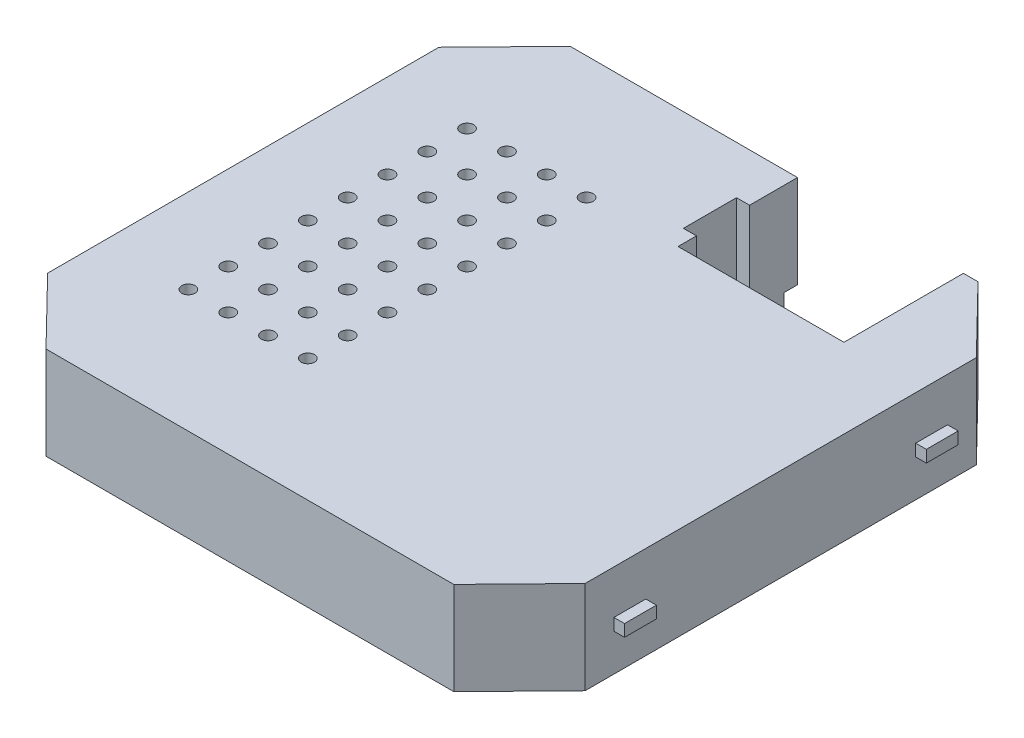
SolidWorks part; units mm, degrees
ref_plane "Front Plane" through (0, 0, 0) normal (0, 0, 1) x (1, 0, 0)
ref_plane "Top Plane" through (0, 0, 0) normal (0, 1, 0) x (1, 0, 0)
ref_plane "Right Plane" through (0, 0, 0) normal (1, 0, 0) x (0, 0, -1)
sketch "Sketch1" plane through (0, 0, 0) normal (0, 1, 0) x (1, 0, 0)
  line L0 (-20.25, 19.75) -> (20.25, 19.75) construction
  line L1 (-20.25, -19.75) -> (20.25, -19.75) construction
  line L2 (20.25, 19.75) -> (20.25, -19.75) construction
  line L3 (20.25, -19.75) -> (-20.25, 19.75) construction
  line L4 (20.25, 19.75) -> (-20.25, -19.75) construction
  line L5 (-20.25, 19.75) -> (-20.25, -19.75) construction
  line L6 (-20.25, 14.7388) -> (-15.3625, 19.75)
  line L7 (-20.25, -14.7388) -> (-15.3625, -19.75)
  line L8 (20.25, -14.7388) -> (15.3625, -19.75)
  line L9 (20.25, 14.7388) -> (15.3625, 19.75)
  line L10 (20.25, -14.7388) -> (20.25, 14.7388)
  line L11 (15.3625, -19.75) -> (-15.3625, -19.75)
  line L12 (-15.3625, 19.75) -> (15.3625, 19.75)
  line L13 (-20.25, 14.7388) -> (-20.25, -14.7388)
  point P5 (0, 0)
  point P13 (0, 0)
  point P14 (0, 0)
  dimension "D1" = 39.5
  dimension "D2" = 40.5
  dimension "D3" = 7
  dimension "D4" = 7
  dimension "D5" = 7
  dimension "D6" = 7
extrude "Boss-Extrude1" add sketch "Sketch1" along normal blind 7
sketch "Sketch2" plane through (0, 0, 0) normal (0, -1, 0) x (1, 0, 0)
  line L44 (14.941, 18.75) -> (-14.941, 18.75)
  line L45 (19.25, 14.3319) -> (14.941, 18.75)
  line L46 (19.25, -14.3319) -> (19.25, 14.3319)
  line L47 (14.941, -18.75) -> (19.25, -14.3319)
  line L48 (-14.941, -18.75) -> (14.941, -18.75)
  line L49 (-19.25, -14.3319) -> (-14.941, -18.75)
  line L50 (-19.25, 14.3319) -> (-19.25, -14.3319)
  line L51 (-14.941, 18.75) -> (-19.25, 14.3319)
  line L52 (14.941, 18.75) -> (-14.941, 18.75)
  line L53 (19.25, 14.3319) -> (14.941, 18.75)
  line L54 (19.25, -14.3319) -> (19.25, 14.3319)
  line L55 (14.941, -18.75) -> (19.25, -14.3319)
  line L56 (-14.941, -18.75) -> (14.941, -18.75)
  line L57 (-19.25, -14.3319) -> (-14.941, -18.75)
  line L58 (-19.25, 14.3319) -> (-19.25, -14.3319)
  line L59 (-14.941, 18.75) -> (-19.25, 14.3319)
  dimension "D1" = 1
extrude "Cut-Extrude1" cut sketch "Sketch2" against normal blind 6
sketch "Sketch3" plane through (0, 7, 0) normal (0, 1, 0) x (1, 0, 0)
  line L0 (15.3625, 19.75) -> (-15.3625, 19.75) construction
  line L1 (14.2625, 19.75) -> (1.7625, 19.75)
  line L2 (14.2625, 19.75) -> (14.2625, 10.75)
  line L3 (14.2625, 10.75) -> (1.7625, 10.75)
  line L5 (1.7625, 19.75) -> (1.7625, 16.137)
  line L6 (1.7625, 16.137) -> (0.7776, 16.137)
  line L7 (0.7776, 16.137) -> (0.7776, 12.137)
  line L8 (0.7776, 12.137) -> (1.7625, 12.137)
  line L9 (1.7625, 12.137) -> (1.7625, 10.75)
  dimension "D1" = 1.1
  dimension "D2" = 9
  dimension "D3" = 12.5
  dimension "D4" = 4
extrude "Cut-Extrude2" cut sketch "Sketch3" against normal through all
sketch "Sketch4" plane through (0, 6, 0) normal (0, -1, 0) x (1, 0, 0)
  line L34 (0.7625, -18.75) -> (1.7625, -18.75)
  line L35 (1.7625, -18.75) -> (1.7625, -16.137)
  line L36 (1.7625, -16.137) -> (0.7776, -16.137)
  line L37 (0.7776, -16.137) -> (0.7776, -12.137)
  line L38 (0.7776, -12.137) -> (1.7625, -12.137)
  line L39 (1.7625, -12.137) -> (1.7625, -10.75)
  line L40 (1.7625, -10.75) -> (14.2625, -10.75)
  line L41 (-0.2224, -17.137) -> (0.7625, -17.137)
  line L42 (-0.2224, -11.137) -> (-0.2224, -17.137)
  line L43 (0.7625, -17.137) -> (0.7625, -18.75)
  line L44 (0.7625, -11.137) -> (-0.2224, -11.137)
  line L45 (0.7625, -9.75) -> (0.7625, -11.137)
  line L46 (15.2625, -18.75) -> (15.2625, -9.75)
  line L47 (15.2625, -9.75) -> (0.7625, -9.75)
  line L48 (-0.2224, -17.137) -> (0.7625, -17.137)
  line L49 (-0.2224, -11.137) -> (-0.2224, -17.137)
  line L50 (0.7625, -17.137) -> (0.7625, -18.75)
  line L51 (0.7625, -11.137) -> (-0.2224, -11.137)
  line L52 (0.7625, -9.75) -> (0.7625, -11.137)
  line L53 (15.2625, -18.75) -> (15.2625, -9.75)
  line L54 (15.2625, -9.75) -> (0.7625, -9.75)
  line L55 (14.2625, -10.75) -> (14.2625, -18.75)
  line L56 (14.2625, -18.75) -> (15.2625, -18.75)
  dimension "D2" = 1
extrude "Boss-Extrude2" add sketch "Sketch4" along normal blind 10
sketch "Sketch5" plane through (-20.25, 0, 0) normal (-1, 0, 0) x (0, 0, 1)
  line L0 (-10.1697, 3.7) -> (-10.1697, 2.8)
  line L1 (-12.8697, 4) -> (-9.8697, 4) construction
  line L2 (-12.8697, 4) -> (-12.8697, 2.5) construction
  line L3 (-12.8697, 2.5) -> (-9.8697, 2.5) construction
  line L4 (-9.8697, 4) -> (-9.8697, 2.5) construction
  line L5 (-12.5697, 2.8) -> (-10.1697, 2.8)
  line L6 (-12.5697, 3.7) -> (-12.5697, 2.8)
  line L7 (-12.5697, 3.7) -> (-10.1697, 3.7)
  line L8 (0, 0) -> (0, 8.3052) construction
  line L11 (12.5697, 3.7) -> (10.1697, 3.7)
  line L12 (12.5697, 3.7) -> (12.5697, 2.8)
  line L13 (12.5697, 2.8) -> (10.1697, 2.8)
  line L14 (10.1697, 3.7) -> (10.1697, 2.8)
  point P18 (0, 0)
  dimension "D1" = 0.3
extrude "Boss-Extrude3" add sketch "Sketch5" along normal blind 0.8
sketch "Sketch6" plane through (20.25, 0, 0) normal (1, 0, 0) x (0, 0, -1)
  line L0 (-12.8697, 4) -> (-12.8697, 2.5) construction
  line L1 (-12.8697, 2.5) -> (-9.8697, 2.5) construction
  line L2 (-9.8697, 2.5) -> (-9.8697, 4) construction
  line L3 (-9.8697, 4) -> (-12.8697, 4) construction
  line L4 (-10.1697, 3.7) -> (-12.5697, 3.7)
  line L5 (-12.5697, 3.7) -> (-12.5697, 2.8)
  line L6 (-12.5697, 2.8) -> (-10.1697, 2.8)
  line L7 (-10.1697, 2.8) -> (-10.1697, 3.7)
  line L8 (0, 0) -> (0, 9.647) construction
  line L9 (10.1697, 2.8) -> (10.1697, 3.7)
  line L10 (12.5697, 2.8) -> (10.1697, 2.8)
  line L11 (12.5697, 3.7) -> (12.5697, 2.8)
  line L12 (10.1697, 3.7) -> (12.5697, 3.7)
  dimension "D1" = 0.3
extrude "Boss-Extrude4" add sketch "Sketch6" along normal blind 0.8
sketch "Sketch7" plane through (0, 7, 0) normal (0, 1, 0) x (1, 0, 0)
  line L0 (11.2047, 0) -> (-23.9034, 0) construction
  line L1 (-13.8841, -1.5) -> (-13.8841, 0) construction
  line L2 (-13.8841, 0) -> (-13.8841, 1.5) construction
  circle A0 centre (-4.8841, -10.5) radius 0.5
  circle A1 centre (-7.8841, -10.5) radius 0.5
  circle A2 centre (-10.8841, -10.5) radius 0.5
  circle A3 centre (-13.8841, -10.5) radius 0.5
  circle A4 centre (-7.8841, -7.5) radius 0.5
  circle A5 centre (-10.8841, -7.5) radius 0.5
  circle A6 centre (-13.8841, -7.5) radius 0.5
  circle A7 centre (-7.8841, -4.5) radius 0.5
  circle A8 centre (-10.8841, -4.5) radius 0.5
  circle A9 centre (-13.8841, -4.5) radius 0.5
  circle A10 centre (-7.8841, -1.5) radius 0.5
  circle A11 centre (-10.8841, -1.5) radius 0.5
  circle A12 centre (-13.8841, -1.5) radius 0.5
  circle A13 centre (-7.8841, 1.5) radius 0.5
  circle A14 centre (-10.8841, 1.5) radius 0.5
  circle A15 centre (-13.8841, 1.5) radius 0.5
  circle A16 centre (-7.8841, 4.5) radius 0.5
  circle A17 centre (-10.8841, 4.5) radius 0.5
  circle A18 centre (-13.8841, 4.5) radius 0.5
  circle A19 centre (-7.8841, 7.5) radius 0.5
  circle A20 centre (-10.8841, 7.5) radius 0.5
  circle A21 centre (-13.8841, 7.5) radius 0.5
  circle A22 centre (-7.8841, 10.5) radius 0.5
  circle A23 centre (-10.8841, 10.5) radius 0.5
  circle A24 centre (-13.8841, 10.5) radius 0.5
  circle A25 centre (-4.8841, -7.5) radius 0.5
  circle A26 centre (-4.8841, -4.5) radius 0.5
  circle A27 centre (-4.8841, -1.5) radius 0.5
  circle A28 centre (-4.8841, 1.5) radius 0.5
  circle A29 centre (-4.8841, 4.5) radius 0.5
  circle A30 centre (-4.8841, 7.5) radius 0.5
  circle A31 centre (-4.8841, 10.5) radius 0.5
  dimension "D1" = 4
  dimension "D3" = 1
  dimension "D2" = 8
extrude "Cut-Extrude3" cut sketch "Sketch7" against normal up to surface (1 mm away) up to face at (1.2126, 6, -6.2979)
